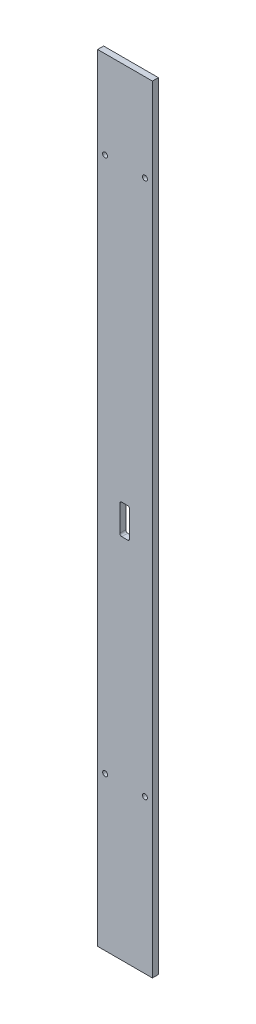
SolidWorks part; units mm, degrees
ref_plane "前视基准面" through (0, 0, 0) normal (0, 0, 1) x (1, 0, 0)
ref_plane "上视基准面" through (0, 0, 0) normal (0, 1, 0) x (1, 0, 0)
ref_plane "右视基准面" through (0, 0, 0) normal (1, 0, 0) x (0, 0, -1)
sketch "草图1" plane through (0, 0, 0) normal (0, 0, 1) x (1, 0, 0)
  line L1 (27.5, -390) -> (-27.5, -390)
  line L2 (27.5, -390) -> (27.5, 390)
  line L3 (27.5, 390) -> (-27.5, 390)
  line L4 (-27.5, -390) -> (-27.5, 390)
  line L5 (27.5, -390) -> (-27.5, 390) construction
  line L6 (27.5, 390) -> (-27.5, -390) construction
  point P0 (0, 0)
  dimension "D1" = 55
  dimension "D2" = 780
extrude "凸台-拉伸1" add sketch "草图1" along normal mid plane 6
sketch "草图4" plane through (0, 0, -3) normal (0, 0, -1) x (-1, 0, 0)
  line L1 (3.252, -21.5794) -> (-2.748, -21.5794)
  line L2 (5.252, -19.5794) -> (5.252, 6.4206)
  line L3 (3.252, 8.4206) -> (-2.748, 8.4206)
  line L4 (-4.748, -19.5794) -> (-4.748, 6.4206)
  arc A0 (-2.748, 8.4206) -> (-4.748, 6.4206) centre (-2.748, 6.4206) ccw
  arc A1 (-2.748, -21.5794) -> (-4.748, -19.5794) centre (-2.748, -19.5794) cw
  arc A2 (5.252, 6.4206) -> (3.252, 8.4206) centre (3.252, 6.4206) ccw
  arc A3 (3.252, -21.5794) -> (5.252, -19.5794) centre (3.252, -19.5794) ccw
  point P10 (-4.748, 8.4206)
  point P13 (-4.748, -21.5794)
  point P14 (5.252, 8.4206)
  dimension "D4" = 2
  dimension "D5" = 2
  dimension "D1" = 10
  dimension "D2" = 30
extrude "切除-拉伸1" cut sketch "草图4" against normal through all
hole_wizard "M6 螺纹孔1" positions "草图6" profile "草图5" tap size "M6" standard "GB"
sketch "草图6" plane through (0, 0, -3) normal (0, 0, -1) x (-1, 0, 0)
  line L0 (0, 390) -> (0, -390) construction
  line L1 (-27.5, 390) -> (27.5, 390) construction
  line L2 (27.5, -390) -> (-27.5, -390) construction
  point P0 (20, 302)
  point P3 (-20, 302)
  point P6 (20, -236)
  point P9 (-20, -236)
  dimension "D1" = 40
  dimension "D2" = 154
  dimension "D3" = 40
  dimension "D4" = 538
sketch "草图5" plane through (-20, 302, -3) normal (1, 0, 0) x (0, 1, 0)
  line L0 (0, 0) -> (0, 18.5022)
  line L1 (0, 18.5022) -> (2.5, 17)
  line L2 (2.5, 17) -> (2.5, 0)
  line L5 (2.5, 0) -> (0, 0)
  line L10 (0, 18.5022) -> (-2.5, 17) construction
  line L11 (0, -6.35) -> (0, 107.95) construction
  dimension "螺纹孔钻头直径" = 5
  dimension "螺纹孔钻头深度" = 17
  dimension "导头角度" = 118
cosmetic thread "孔螺蚊线1" parameters "D1"=6, "D2"=6
cosmetic thread "孔螺蚊线2" parameters "D1"=6, "D2"=6
cosmetic thread "孔螺蚊线3" parameters "D1"=6, "D2"=6
cosmetic thread "孔螺蚊线4" parameters "D1"=6, "D2"=6
